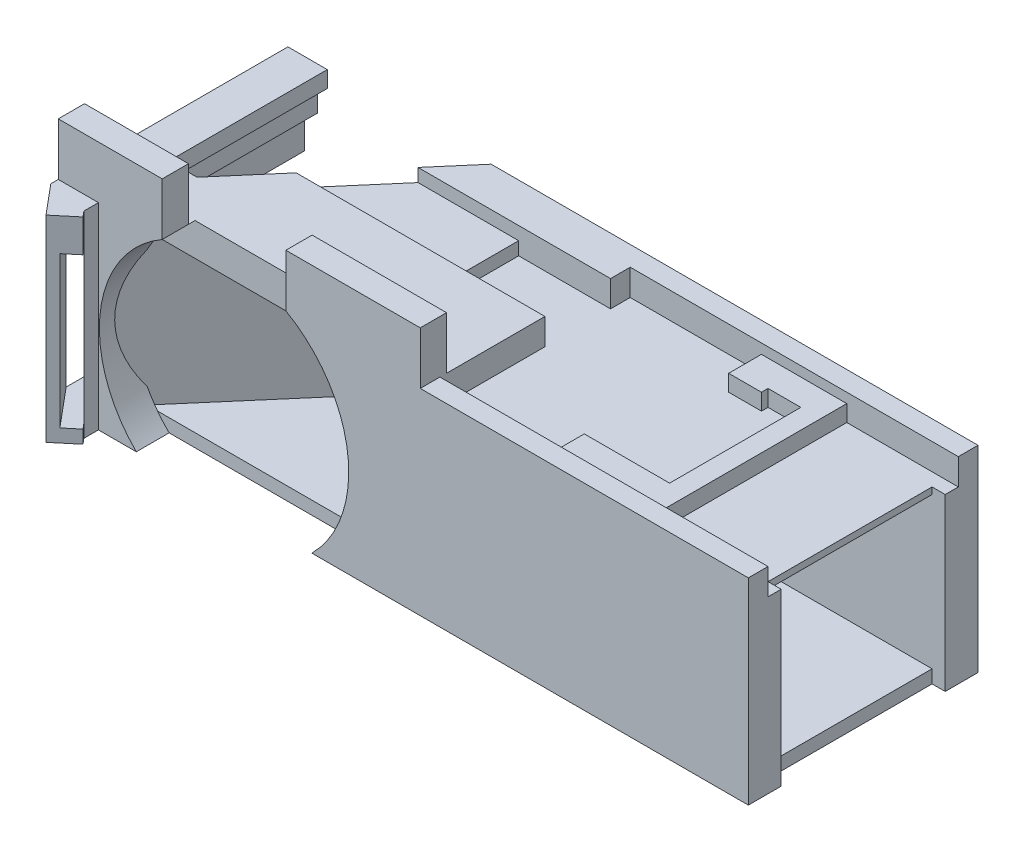
SolidWorks part; units mm, degrees
ref_plane "Front Plane" through (0, 0, 0) normal (0, 0, 1) x (1, 0, 0)
ref_plane "Top Plane" through (0, 0, 0) normal (0, 1, 0) x (1, 0, 0)
ref_plane "Right Plane" through (0, 0, 0) normal (1, 0, 0) x (0, 0, -1)
sketch "Sketch1" plane through (0, 0, 0) normal (0, 1, 0) x (1, 0, 0)
  line L0 (-20.9122, 13.018) -> (-20.9122, 48.018)
  line L1 (-20.9122, 48.018) -> (-75.9122, 48.018)
  line L2 (-75.9122, 48.018) -> (-105.9122, 13.018)
  line L3 (-105.9122, 13.018) -> (-20.9122, 13.018)
  line L4 (-105.9122, 13.018) -> (-65.9122, 13.018)
  line L6 (-110.1779, 11.8828) -> (-110.1779, 48.018)
  line L8 (-105.9122, 48.018) -> (-75.9122, 48.018)
  line L9 (-105.9122, 16.8595) -> (-79.2049, 48.018)
  line L10 (-105.9122, 13.018) -> (-103.3452, 9.9504)
  line L11 (-103.3452, 9.9504) -> (-106.4128, 7.3834)
  line L12 (-106.4128, 7.3834) -> (-110.1779, 11.8828)
  line L13 (-110.1779, 11.8828) -> (-105.9122, 16.8595)
  line L14 (-110.1779, 48.018) -> (-105.9122, 48.018)
  line L15 (-104.1779, 48.018) -> (-104.1779, 18.8828)
  dimension "D2" = 55
  dimension "D3" = 35
  dimension "D6" = 2.5
  dimension "D7" = 6
  dimension "D8" = 4
  dimension "D9" = 4
sketch "Sketch2" plane through (0, 0, 0) normal (0, 1, 0) x (1, 0, 0)
  line L0 (-105.9122, 13.018) -> (-20.9122, 13.018)
  line L1 (-20.9122, 13.018) -> (-20.9122, 48.018)
  line L2 (-20.9122, 48.018) -> (-75.9122, 48.018)
  line L3 (-75.9122, 48.018) -> (-105.9122, 13.018)
sketch "Sketch3" plane through (0, 0, 0) normal (0, 1, 0) x (1, 0, 0)
  line L0 (-106.4128, 7.3834) -> (-110.1779, 11.8828)
  line L1 (-110.1779, 11.8828) -> (-79.2049, 48.018)
  line L2 (-79.2049, 48.018) -> (-75.9122, 48.018)
  line L3 (-75.9122, 48.018) -> (-105.9122, 13.018)
  line L4 (-105.9122, 13.018) -> (-103.3452, 9.9504)
  line L5 (-103.3452, 9.9504) -> (-106.4128, 7.3834)
sketch "Sketch4" plane through (0, 0, 0) normal (0, 1, 0) x (1, 0, 0)
  line L0 (-110.1779, 11.8828) -> (-110.1779, 48.018)
  line L1 (-110.1779, 48.018) -> (-104.1779, 48.018)
  line L2 (-104.1779, 48.018) -> (-104.1779, 18.8828)
  line L3 (-104.1779, 18.8828) -> (-110.1779, 11.8828)
extrude "Boss-Extrude3" add sketch "Sketch2" along normal blind 30
sketch "Sketch6" plane through (-20.9122, 0, 0) normal (1, 0, 0) x (0, 0, -1)
  line L1 (43.018, 2) -> (18.018, 2)
  line L2 (43.018, 2) -> (43.018, 25)
  line L3 (43.018, 25) -> (18.018, 25)
  line L4 (18.018, 2) -> (18.018, 25)
  line L5 (43.018, 2) -> (18.018, 25) construction
  line L6 (43.018, 25) -> (18.018, 2) construction
  line L7 (13.018, 30) -> (13.018, 0) construction
  line L8 (48.018, 30) -> (48.018, 0) construction
  line L9 (13.018, 0) -> (48.018, 0) construction
  line L10 (13.018, 30) -> (48.018, 30) construction
  point P0 (30.518, 13.5)
  dimension "D1" = 5
  dimension "D2" = 5
  dimension "D3" = 2
  dimension "D4" = 5
extrude "Cut-Extrude1" cut sketch "Sketch6" against normal through all
sketch "Sketch7" plane through (-20.9122, 0, 0) normal (1, 0, 0) x (0, 0, -1)
  line L0 (13.018, 30) -> (48.018, 30) construction
  line L1 (18.018, 25) -> (43.018, 25)
  line L2 (18.018, 25) -> (18.018, 30)
  line L3 (18.018, 30) -> (43.018, 30)
  line L4 (43.018, 25) -> (43.018, 30)
extrude "Cut-Extrude2" cut sketch "Sketch7" against normal blind 7.5
sketch "Sketch8" plane through (-20.9122, 0, 0) normal (1, 0, 0) x (0, 0, -1)
  line L0 (13.018, 0) -> (48.018, 0) construction
  line L1 (18.018, 2) -> (43.018, 2)
  line L2 (18.018, 2) -> (18.018, 0)
  line L3 (18.018, 0) -> (43.018, 0)
  line L4 (43.018, 2) -> (43.018, 0)
extrude "Cut-Extrude3" cut sketch "Sketch8" against normal blind 1
sketch "Sketch9" plane through (0, 0, -13.018) normal (0, 0, 1) x (1, 0, 0)
  line L0 (-105.9122, 30) -> (-20.9122, 30) construction
  line L3 (-105.9122, 30) -> (-105.9122, 0) construction
  circle A0 centre (-84.9122, 13.5) radius 19
  dimension "D1" = 16.5
  dimension "D2" = 21
extrude "Cut-Extrude4" cut sketch "Sketch9" against normal blind 5
extrude "Boss-Extrude4" add sketch "Sketch3" along normal blind 30
sketch "Sketch10" plane through (0, 0, -13.018) normal (0, 0, 1) x (1, 0, 0)
  line L0 (-105.9122, 30) -> (-94.3329, 30) construction
  line L1 (-104.0556, 30) -> (-105.9122, 30)
  line L2 (-104.0556, 30) -> (-104.0556, 0)
  line L3 (-104.0556, 0) -> (-105.9122, 0)
  line L4 (-105.9122, 30) -> (-105.9122, 0)
extrude "Boss-Extrude5" add sketch "Sketch10" along normal blind 3
extrude "Boss-Extrude6" add sketch "Sketch4" along normal blind 30
sketch "Sketch11" plane through (-47.4594, 0, -56.7155) normal (0.6418, 0, 0.7669) x (0.7669, 0, -0.6418)
  line L0 (-72.8711, 30) -> (-72.8711, 0) construction
  line L1 (-75.3711, 25) -> (-72.8711, 25)
  line L2 (-75.3711, 25) -> (-75.3711, 2)
  line L3 (-75.3711, 2) -> (-72.8711, 2)
  line L4 (-72.8711, 25) -> (-72.8711, 2)
  line L5 (-76.8711, 30) -> (-72.8711, 30) construction
  line L6 (-76.8711, 0) -> (-70.4058, 0) construction
  dimension "D1" = 2.5
  dimension "D2" = 5
  dimension "D3" = 2
extrude "Cut-Extrude5" cut sketch "Sketch11" against normal through all
sketch "Sketch12" plane through (-104.1779, 0, 0) normal (1, 0, 0) x (0, 0, -1)
  line L0 (48.018, 30) -> (48.018, 0) construction
  line L1 (18.8828, 27.5) -> (48.018, 27.5)
  line L2 (18.8828, 27.5) -> (18.8828, 2.5)
  line L3 (18.8828, 2.5) -> (48.018, 2.5)
  line L4 (48.018, 27.5) -> (48.018, 2.5)
  line L5 (18.8828, 30) -> (18.8828, 0) construction
  line L6 (18.8828, 30) -> (48.018, 30) construction
  dimension "D1" = 25
  dimension "D2" = 2.5
extrude "Cut-Extrude6" cut sketch "Sketch12" against normal blind 3.5
sketch "Sketch13" plane through (-107.6779, 0, 0) normal (1, 0, 0) x (0, 0, -1)
  line L0 (48.018, 27.5) -> (18.8828, 27.5) construction
  line L1 (28.8828, 17.5) -> (48.018, 17.5)
  line L2 (28.8828, 17.5) -> (28.8828, 12.5)
  line L3 (28.8828, 12.5) -> (48.018, 12.5)
  line L4 (48.018, 17.5) -> (48.018, 12.5)
  line L5 (18.8828, 2.5) -> (48.018, 2.5) construction
  line L6 (18.8828, 27.5) -> (18.8828, 2.5) construction
  line L7 (48.018, 2.5) -> (48.018, 27.5) construction
  dimension "D1" = 10
  dimension "D2" = 10
  dimension "D3" = 10
extrude "Cut-Extrude7" cut sketch "Sketch13" against normal through all
sketch "Sketch14" plane through (-107.6779, 0, 0) normal (1, 0, 0) x (0, 0, -1)
  line L0 (48.018, 27.5) -> (18.8828, 27.5) construction
  line L1 (18.8828, 23.5) -> (48.018, 23.5)
  line L2 (18.8828, 23.5) -> (18.8828, 27.5)
  line L3 (18.8828, 27.5) -> (48.018, 27.5)
  line L4 (48.018, 23.5) -> (48.018, 27.5)
  line L5 (48.018, 17.5) -> (48.018, 27.5) construction
  line L6 (18.8828, 27.5) -> (18.8828, 2.5) construction
  point P11 (33.4504, 23.5)
  dimension "D1" = 4
extrude "Boss-Extrude7" add sketch "Sketch14" along normal blind 2
sketch "Sketch16" plane through (-107.6779, 0, 0) normal (1, 0, 0) x (0, 0, -1)
  line L0 (18.8828, 2.5) -> (48.018, 2.5) construction
  line L1 (18.8828, 4) -> (48.018, 4)
  line L2 (18.8828, 4) -> (18.8828, 2.5)
  line L3 (18.8828, 2.5) -> (48.018, 2.5)
  line L4 (48.018, 4) -> (48.018, 2.5)
  line L5 (18.8828, 23.5) -> (18.8828, 2.5) construction
  line L6 (48.018, 2.5) -> (48.018, 12.5) construction
  dimension "D1" = 1.5
extrude "Boss-Extrude8" add sketch "Sketch16" along normal blind 2
sketch "Sketch17" plane through (0, 0, -18.8828) normal (0, 0, -1) x (-1, 0, 0)
  line L0 (104.1779, 27.5) -> (104.1779, 2.5) construction
  line L1 (101.6264, 30) -> (104.1779, 30)
  line L2 (101.6264, 30) -> (101.6264, 0)
  line L3 (101.6264, 0) -> (104.1779, 0)
  line L4 (104.1779, 30) -> (104.1779, 0)
  line L5 (101.6264, 4.4649) -> (101.6264, 2) construction
  line L6 (94.3329, 30) -> (75.4914, 30) construction
  dimension "D1" = 30
extrude "Boss-Extrude9" add sketch "Sketch17" along normal blind 5
sketch "Sketch18" plane through (-104.1779, 0, 0) normal (1, 0, 0) x (0, 0, -1)
  line L1 (48.018, 2.5) -> (18.8828, 2.5)
  line L2 (48.018, 2.5) -> (48.018, 0)
  line L3 (48.018, 0) -> (18.8828, 0)
  line L4 (18.8828, 2.5) -> (18.8828, 0)
extrude "Boss-Extrude10" add sketch "Sketch18" along normal up to surface (24.9731 mm away)
sketch "Sketch19" plane through (-67.4877, 0, -57.8466) normal (0.7593, 0, 0.6508) x (0.6508, 0, -0.7593)
  line L0 (-19.5304, 25) -> (-52.4573, 25) construction
  line L1 (-32.9673, 25) -> (-30.4788, 25)
  line L2 (-32.9673, 25) -> (-32.9673, 2)
  line L3 (-32.9673, 2) -> (-30.4788, 2)
  line L4 (-30.4788, 25) -> (-30.4788, 2)
  line L5 (-52.4573, 2) -> (-19.5304, 2) construction
extrude "Boss-Extrude11" add sketch "Sketch19" along normal blind 2
sketch "Sketch20" plane through (-19.8353, 0, 23.1412) normal (0.6508, 0, -0.7593) x (-0.7593, 0, -0.6508)
  line L1 (88.8865, 25) -> (86.8865, 25)
  line L2 (88.8865, 25) -> (88.8865, 2)
  line L3 (88.8865, 2) -> (86.8865, 2)
  line L4 (86.8865, 25) -> (86.8865, 2)
extrude "Cut-Extrude8" cut sketch "Sketch20" against normal up to surface and the other way up to surface
sketch "Sketch21" plane through (-101.6264, 0, 0) normal (1, 0, 0) x (0, 0, -1)
  line L0 (21.8595, 30) -> (21.8595, 2.5) construction
  line L1 (21.8595, 30) -> (23.8828, 30)
  line L2 (21.8595, 30) -> (21.8595, 2.5)
  line L3 (21.8595, 2.5) -> (23.8828, 2.5)
  line L4 (23.8828, 30) -> (23.8828, 2.5)
  line L5 (23.8828, 30) -> (21.8595, 30) construction
extrude "Boss-Extrude12" add sketch "Sketch21" along normal up to surface (1.7342 mm away)
sketch "Sketch22" plane through (-20.9122, 0, 0) normal (1, 0, 0) x (0, 0, -1)
  line L1 (13.018, 30) -> (48.018, 30)
  line L2 (13.018, 30) -> (13.018, 0)
  line L3 (13.018, 0) -> (48.018, 0)
  line L4 (48.018, 30) -> (48.018, 0)
extrude "Boss-Extrude13" add sketch "Sketch22" along normal blind 15.9 and the other way up to vertex (7.5 mm away)
sketch "Sketch23" plane through (-28.4122, 0, 0) normal (-1, 0, 0) x (0, 0, 1)
  line L0 (-18.018, 25) -> (-43.018, 25) construction
  line L1 (-43.018, 25) -> (-18.018, 25)
  line L2 (-43.018, 25) -> (-43.018, 2)
  line L3 (-43.018, 2) -> (-18.018, 2)
  line L4 (-18.018, 25) -> (-18.018, 2)
extrude "Cut-Extrude9" cut sketch "Sketch23" against normal through all
sketch "Sketch24" plane through (-5.0122, 0, 0) normal (1, 0, 0) x (0, 0, -1)
  line L0 (48.018, 30) -> (13.018, 30) construction
  line L1 (43.018, 30) -> (18.018, 30)
  line L2 (43.018, 30) -> (43.018, 25)
  line L3 (43.018, 25) -> (18.018, 25)
  line L4 (18.018, 30) -> (18.018, 25)
extrude "Cut-Extrude10" cut sketch "Sketch24" against normal blind 2
sketch "Sketch25" plane through (0, 30, 0) normal (0, 1, 0) x (1, 0, 0)
  line L1 (-5.0122, 16.018) -> (-55.0122, 16.018)
  line L2 (-5.0122, 16.018) -> (-5.0122, 45.018)
  line L3 (-5.0122, 45.018) -> (-55.0122, 45.018)
  line L4 (-55.0122, 16.018) -> (-55.0122, 45.018)
  line L5 (-75.4914, 13.018) -> (-5.0122, 13.018) construction
  line L6 (-5.0122, 48.018) -> (-79.2049, 48.018) construction
  line L7 (-5.0122, 18.018) -> (-5.0122, 13.018) construction
  dimension "D1" = 3
  dimension "D2" = 3
  dimension "D3" = 50
extrude "Cut-Extrude11" cut sketch "Sketch25" against normal blind 4
sketch "Sketch26" plane through (0, 26, 0) normal (0, 1, 0) x (1, 0, 0)
  line L0 (-55.0122, 16.018) -> (-5.0122, 16.018) construction
  line L1 (-22.0122, 16.018) -> (-25.0122, 16.018)
  line L2 (-22.0122, 16.018) -> (-22.0122, 45.018)
  line L3 (-22.0122, 45.018) -> (-25.0122, 45.018)
  line L4 (-25.0122, 16.018) -> (-25.0122, 45.018)
  line L5 (-5.0122, 45.018) -> (-55.0122, 45.018) construction
  line L6 (-5.0122, 16.018) -> (-5.0122, 18.018) construction
  point P10 (-5.0122, 17.018)
  dimension "D1" = 17
  dimension "D2" = 20
extrude "Boss-Extrude14" add sketch "Sketch26" along normal blind 2.5
sketch "Sketch27" plane through (0, 26, 0) normal (0, 1, 0) x (1, 0, 0)
  line L0 (-25.0122, 45.018) -> (-55.0122, 45.018) construction
  line L1 (-35.0122, 40.018) -> (-30.0122, 40.018)
  line L2 (-35.0122, 40.018) -> (-35.0122, 45.018)
  line L3 (-35.0122, 45.018) -> (-30.0122, 45.018)
  line L4 (-30.0122, 40.018) -> (-30.0122, 45.018)
  line L5 (-5.0122, 43.018) -> (-5.0122, 45.018) construction
  dimension "D1" = 5
  dimension "D2" = 25
  dimension "D3" = 30
extrude "Boss-Extrude15" add sketch "Sketch27" along normal blind 2.5
sketch "Sketch28" plane through (-30.0122, 0, 0) normal (1, 0, 0) x (0, 0, -1)
  line L0 (40.018, 28.5) -> (45.018, 28.5) construction
  line L1 (45.018, 26) -> (41.018, 26)
  line L2 (45.018, 26) -> (45.018, 28.5)
  line L3 (45.018, 28.5) -> (41.018, 28.5)
  line L4 (41.018, 26) -> (41.018, 28.5)
  line L5 (40.018, 26) -> (45.018, 26) construction
  line L6 (45.018, 28.5) -> (45.018, 26) construction
  dimension "D1" = 4
extrude "Boss-Extrude16" add sketch "Sketch28" along normal up to next
sketch "Sketch29" plane through (0, 26, 0) normal (0, 1, 0) x (1, 0, 0)
  line L0 (-5.0122, 16.018) -> (-5.0122, 18.018) construction
  line L1 (-38.0122, 21.018) -> (-25.0122, 21.018)
  line L2 (-38.0122, 21.018) -> (-38.0122, 16.018)
  line L3 (-38.0122, 16.018) -> (-25.0122, 16.018)
  line L4 (-25.0122, 21.018) -> (-25.0122, 16.018)
  dimension "D1" = 5
  dimension "D2" = 33
extrude "Boss-Extrude17" add sketch "Sketch29" along normal blind 2.5
sketch "Sketch30" plane through (-55.0122, 0, 0) normal (1, 0, 0) x (0, 0, -1)
  line L0 (45.018, 30) -> (16.018, 30) construction
  line L1 (42.018, 30) -> (32.018, 30)
  line L2 (42.018, 30) -> (42.018, 26)
  line L3 (42.018, 26) -> (32.018, 26)
  line L4 (32.018, 30) -> (32.018, 26)
  line L5 (45.018, 26) -> (16.018, 26) construction
  line L6 (45.018, 26) -> (45.018, 30) construction
  dimension "D1" = 3
  dimension "D2" = 10
extrude "Cut-Extrude12" cut sketch "Sketch30" against normal blind 14
sketch "Sketch31" plane through (-69.0122, 0, 0) normal (1, 0, 0) x (0, 0, -1)
  line L0 (42.018, 30) -> (32.018, 30) construction
  line L1 (32.018, 30) -> (42.018, 30)
  line L2 (32.018, 30) -> (32.018, 28)
  line L3 (32.018, 28) -> (42.018, 28)
  line L4 (42.018, 30) -> (42.018, 28)
  line L5 (42.018, 26) -> (42.018, 30) construction
extrude "Cut-Extrude13" cut sketch "Sketch31" against normal up to next
sketch "Sketch32" plane through (0, 26, 0) normal (0, 1, 0) x (1, 0, 0)
  line L1 (-7.0122, 18.018) -> (-5.0122, 18.018)
  line L2 (-7.0122, 18.018) -> (-7.0122, 43.018)
  line L3 (-7.0122, 43.018) -> (-5.0122, 43.018)
  line L4 (-5.0122, 18.018) -> (-5.0122, 43.018)
extrude "Cut-Extrude14" cut sketch "Sketch32" against normal through all
sketch "Sketch33" plane through (0, 30, 0) normal (0, 1, 0) x (1, 0, 0)
  line L0 (-75.4914, 13.018) -> (-5.0122, 13.018) construction
  line L1 (-55.0122, 13.018) -> (-75.4914, 13.018)
  line L2 (-55.0122, 13.018) -> (-55.0122, 17.018)
  line L3 (-55.0122, 17.018) -> (-75.4914, 17.018)
  line L4 (-75.4914, 13.018) -> (-75.4914, 17.018)
  line L5 (-75.4914, 13.018) -> (-75.4914, 18.018) construction
  dimension "D1" = 4
extrude "Boss-Extrude18" add sketch "Sketch33" along normal blind 8
sketch "Sketch34" plane through (0, 30, 0) normal (0, 1, 0) x (1, 0, 0)
  line L0 (-110.1779, 48.018) -> (-110.1779, 11.8828) construction
  line L1 (-94.3329, 13.018) -> (-110.1779, 13.018)
  line L2 (-94.3329, 13.018) -> (-94.3329, 17.018)
  line L3 (-94.3329, 17.018) -> (-110.1779, 17.018)
  line L4 (-110.1779, 13.018) -> (-110.1779, 17.018)
  dimension "D1" = 4
extrude "Boss-Extrude19" add sketch "Sketch34" along normal blind 8
